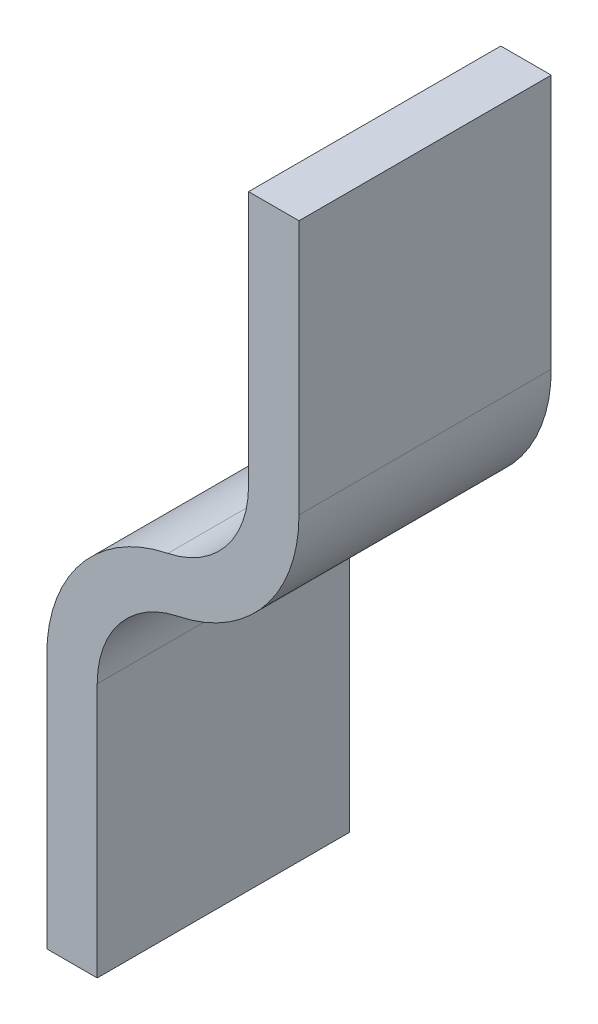
SolidWorks part; units mm, degrees
ref_plane "Front Plane" through (0, 0, 0) normal (0, 0, 1) x (1, 0, 0)
ref_plane "Top Plane" through (0, 0, 0) normal (0, 1, 0) x (1, 0, 0)
ref_plane "Right Plane" through (0, 0, 0) normal (1, 0, 0) x (0, 0, -1)
sketch "Sketch1" plane through (0, 0, 0) normal (0, 0, 1) x (1, 0, 0)
  line L0 (0, 0) -> (2, 0)
  line L1 (2, 0) -> (2, -10.101)
  line L2 (0, 0) -> (0, -10.101)
  line L3 (-8, -19.899) -> (-8, -30)
  line L4 (-6, -30) -> (-6, -19.899)
  line L5 (-8, -30) -> (-6, -30)
  arc A0 (0, -10.101) -> (-3.2, -14.0202) centre (-4, -10.101) cw
  arc A1 (2, -10.101) -> (-2.8, -15.9798) centre (-4, -10.101) cw
  arc A2 (-6, -19.899) -> (-2.8, -15.9798) centre (-2, -19.899) cw
  arc A3 (-8, -19.899) -> (-3.2, -14.0202) centre (-2, -19.899) cw
  dimension "D1" = 2
  dimension "D2" = 30
  dimension "D3" = 10
  dimension "D4" = 2
extrude "Boss-Extrude2" add sketch "Sketch1" against normal blind 10
